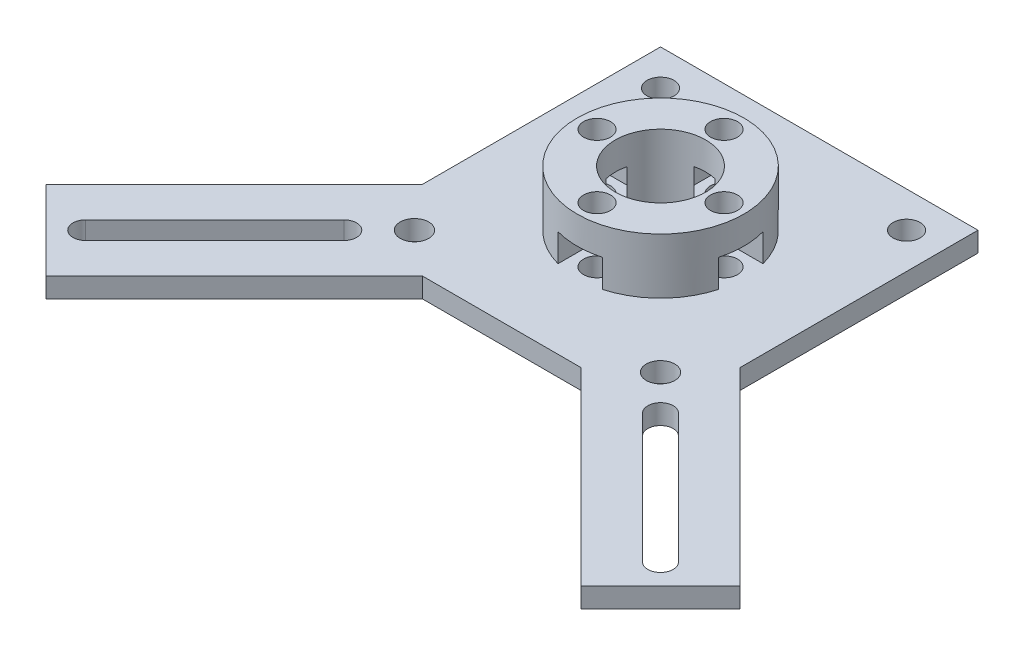
SolidWorks part; units mm, degrees
ref_plane "前视基准面" through (0, 0, 0) normal (0, 0, 1) x (1, 0, 0)
ref_plane "上视基准面" through (0, 0, 0) normal (0, 1, 0) x (1, 0, 0)
ref_plane "右视基准面" through (0, 0, 0) normal (1, 0, 0) x (0, 0, -1)
sketch "草图1" plane through (0, 0, 0) normal (0, 1, 0) x (1, 0, 0)
  line L3 (-10, -20) -> (10, -20)
  line L6 (-20, -10) -> (-43.7132, -33.7132)
  line L7 (-10, -20) -> (-33.7132, -43.7132)
  line L8 (10, -20) -> (33.8446, -43.8446)
  line L9 (20, -10) -> (43.8446, -33.8446)
  line L10 (-43.7132, -33.7132) -> (-33.7132, -43.7132)
  line L11 (33.8446, -43.8446) -> (43.8446, -33.8446)
  line L12 (-19.9497, -19.9497) -> (-36.2132, -36.2132) construction
  line L13 (-18.8184, -21.0811) -> (-35.0818, -37.3446)
  line L14 (-21.0811, -18.8184) -> (-37.3446, -35.0818)
  line L15 (19.9497, -19.9497) -> (36.2132, -36.2132) construction
  line L16 (21.0811, -18.8184) -> (37.3446, -35.0818)
  line L17 (18.8184, -21.0811) -> (35.0818, -37.3446)
  line L20 (-20, -10) -> (-20, 20)
  line L21 (-20, 20) -> (20, 20)
  line L22 (20, 20) -> (20, -10)
  circle A0 centre (-15.5, 15.5) radius 1.7
  circle A1 centre (15.5, 15.5) radius 1.7
  circle A2 centre (-15.5, -15.5) radius 1.8
  circle A3 centre (15.5, -15.5) radius 1.8
  arc A6 (-18.8184, -21.0811) -> (-21.0811, -18.8184) centre (-19.9497, -19.9497) ccw
  arc A7 (-37.3446, -35.0818) -> (-35.0818, -37.3446) centre (-36.2132, -36.2132) ccw
  circle A8 centre (0, 0) radius 5.7
  circle A9 centre (-8, 0) radius 1.7
  circle A10 centre (0, 8) radius 1.7
  circle A11 centre (8, 0) radius 1.7
  circle A12 centre (0, -8) radius 1.7
  arc A13 (21.0811, -18.8184) -> (18.8184, -21.0811) centre (19.9497, -19.9497) ccw
  arc A14 (35.0818, -37.3446) -> (37.3446, -35.0818) centre (36.2132, -36.2132) ccw
  point P34 (-33.1606, -34.0237)
  point P38 (-28.0815, -28.0815)
  point P43 (28.0815, -28.0815)
extrude "凸台-拉伸1" add sketch "草图1" along normal blind 2.5
sketch "草图2" plane through (0, 2.5, 0) normal (0, 1, 0) x (1, 0, 0)
  circle A0 centre (0, 0) radius 10.5
extrude "凸台-拉伸2" add sketch "草图2" along normal blind 7
sketch "草图4" plane through (0, 2.5, 0) normal (0, -1, 0) x (1, 0, 0)
  circle A1 centre (0, -8) radius 1.7
  circle A2 centre (-8, 0) radius 1.7
  circle A3 centre (8, 0) radius 1.7
  circle A4 centre (0, 8) radius 1.7
extrude "切除-拉伸1" cut sketch "草图4" against normal blind 7
sketch "草图5" plane through (0, 2.5, 0) normal (0, 1, 0) x (1, 0, 0)
  line L1 (-4.7668, 0) -> (-6.3834, 2.8)
  line L2 (-6.3834, 2.8) -> (-11.2332, 2.8)
  line L5 (-11.2332, -2.8) -> (-6.3834, -2.8)
  line L6 (-6.3834, -2.8) -> (-4.7668, 0)
  line L7 (4.7668, 0) -> (6.3834, -2.8)
  line L8 (6.3834, -2.8) -> (11.2332, -2.8)
  line L11 (11.2332, 2.8) -> (6.3834, 2.8)
  line L12 (6.3834, 2.8) -> (4.7668, 0)
  line L14 (-2.8, 11.2332) -> (-2.8, 6.3834)
  line L15 (-2.8, 6.3834) -> (0, 4.7668)
  line L16 (0, 4.7668) -> (2.8, 6.3834)
  line L17 (2.8, 6.3834) -> (2.8, 11.2332)
  line L19 (0, -4.7668) -> (-2.8, -6.3834)
  line L20 (-2.8, -6.3834) -> (-2.8, -11.2332)
  line L23 (2.8, -11.2332) -> (2.8, -6.3834)
  line L24 (2.8, -6.3834) -> (0, -4.7668)
  line L25 (-11.2332, 2.8) -> (-11.2332, -2.8)
  line L29 (-2.8, 11.2332) -> (2.8, 11.2332)
  line L32 (11.2332, 2.8) -> (11.2332, -2.8)
  line L35 (-2.8, -11.2332) -> (2.8, -11.2332)
  line L39 (-1.4, -10.4249) -> (0, -11.2332) [skipped]
  line L40 (1.4, -10.4249) -> (2.8, -9.6166) [skipped]
  line L41 (9.6166, -2.8) -> (10.4249, -1.4) [skipped]
  line L42 (11.2332, 0) -> (10.4249, 1.4) [skipped]
  line L43 (1.4, 10.4249) -> (0, 11.2332) [skipped]
  line L44 (0, 11.2332) -> (-1.4, 10.4249) [skipped]
  line L45 (-10.4249, -1.4) -> (-9.6166, -2.8) [skipped]
  line L46 (-9.6166, 2.8) -> (-10.4249, 1.4) [skipped]
extrude "切除-拉伸2" cut sketch "草图5" along normal blind 3.5
sketch "草图6" plane through (0, 2.5, 0) normal (0, -1, 0) x (1, 0, 0)
  circle A0 centre (0, 0) radius 5.7
extrude "切除-拉伸3" cut sketch "草图6" against normal blind 20
